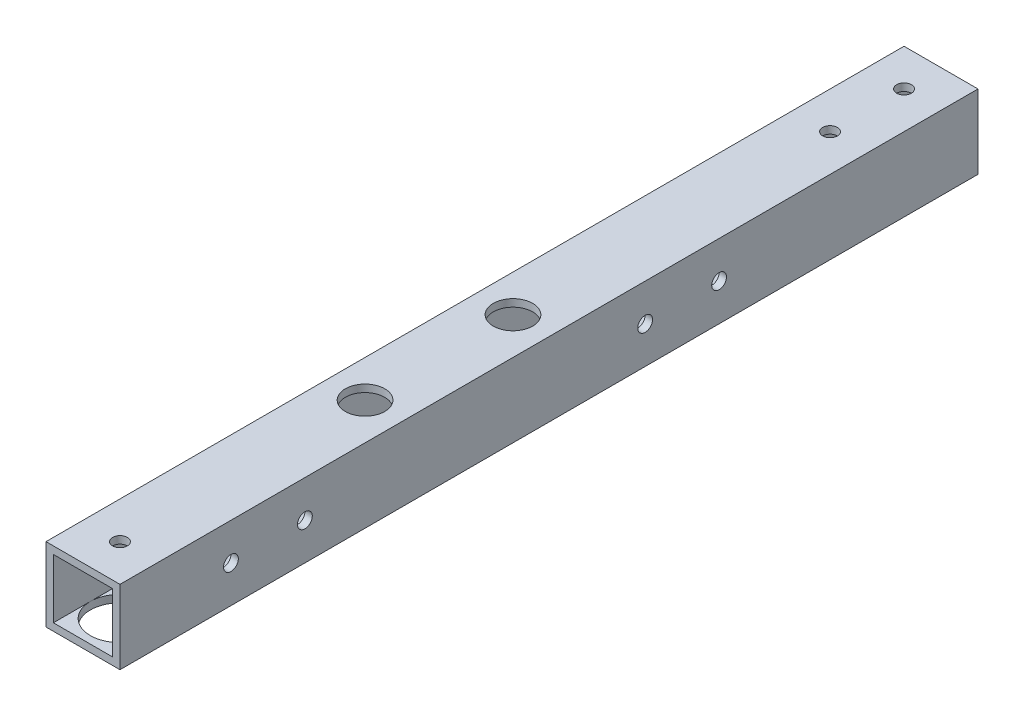
SolidWorks part; units mm, degrees
material "1060 合金"
ref_plane "正面" through (0, 0, 0) normal (0, 0, 1) x (1, 0, 0)
ref_plane "平面" through (0, 0, 0) normal (0, 1, 0) x (1, 0, 0)
ref_plane "右側面" through (0, 0, 0) normal (1, 0, 0) x (0, 0, -1)
sketch "ｽｹｯﾁ1" plane through (0, 0, 0) normal (0, 0, 1) x (1, 0, 0)
  line L1 (-7.0101, 7.7326) -> (7.9899, 7.7326)
  line L2 (-7.0101, 7.7326) -> (-7.0101, -7.2674)
  line L3 (-7.0101, -7.2674) -> (7.9899, -7.2674)
  line L4 (7.9899, 7.7326) -> (7.9899, -7.2674)
  line L9 (-5.5101, 6.2326) -> (6.4899, 6.2326)
  line L10 (-5.5101, 6.2326) -> (-5.5101, -5.7674)
  line L11 (-5.5101, -5.7674) -> (6.4899, -5.7674)
  line L12 (6.4899, 6.2326) -> (6.4899, -5.7674)
  dimension "D1" = 15
  dimension "D2" = 15
  dimension "D3" = 1.5
  dimension "D4" = 1.5
  dimension "D5" = 12
  dimension "D6" = 12
extrude "ﾎﾞｽ - 押し出し2" add sketch "ｽｹｯﾁ1" along normal blind 174
sketch "ｽｹｯﾁ3" plane through (7.9899, 0, 0) normal (1, 0, 0) x (0, 0, -1)
  line L0 (0, 0.2326) -> (-52.5, 0.2326)
  line L1 (0, -7.2674) -> (0, 7.7326) construction
  circle A0 centre (-52.5, 0.2326) radius 1.5
  dimension "D2" = 3
  dimension "D1" = 52.5
extrude "ｶｯﾄ - 押し出し2" cut sketch "ｽｹｯﾁ3" against normal blind 10
sketch "ｽｹｯﾁ6" plane through (-7.0101, 0, 0) normal (-1, 0, 0) x (0, 0, 1)
  line L0 (0, 0.2326) -> (52.5, 0.2326)
  line L1 (0, 7.7326) -> (0, -7.2674) construction
  circle A0 centre (52.5, 0.2326) radius 4
  dimension "D1" = 52.5
extrude "ｶｯﾄ - 押し出し4" cut sketch "ｽｹｯﾁ6" against normal blind 10
sketch "ｽｹｯﾁ7" plane through (7.9899, 0, 0) normal (1, 0, 0) x (0, 0, -1)
  line L0 (-174, 0.2326) -> (-151.5, 0.2326)
  line L1 (-174, -7.2674) -> (-174, 7.7326) construction
  circle A0 centre (-151.5, 0.2326) radius 1.5
  dimension "D1" = 22.5
extrude "ｶｯﾄ - 押し出し5" cut sketch "ｽｹｯﾁ7" against normal blind 10
sketch "ｽｹｯﾁ8" plane through (-7.0101, 0, 0) normal (-1, 0, 0) x (0, 0, 1)
  line L0 (174, 0.2326) -> (151.5, 0.2326)
  line L1 (174, 7.7326) -> (174, -7.2674) construction
  circle A0 centre (151.5, 0.2326) radius 4
  dimension "D1" = 22.5
extrude "ｶｯﾄ - 押し出し6" cut sketch "ｽｹｯﾁ8" against normal blind 10
sketch "ｽｹｯﾁ10" plane through (-7.0101, 0, 0) normal (-1, 0, 0) x (0, 0, 1)
  line L0 (0, 0.2326) -> (86.8, 0.2326)
  line L1 (0, 7.7326) -> (0, -7.2674) construction
  circle A0 centre (86.8, 0.2326) radius 1.5
  dimension "D2" = 3
  dimension "D1" = 86.8
extrude "ｶｯﾄ - 押し出し9" cut sketch "ｽｹｯﾁ10" against normal blind 10
sketch "ｽｹｯﾁ13" plane through (-7.0101, 0, 0) normal (-1, 0, 0) x (0, 0, 1)
  line L0 (86.8, 0.2326) -> (116.8, 0.2326)
  circle A0 centre (116.8, 0.2326) radius 1.5
  dimension "D1" = 30
extrude "ｶｯﾄ - 押し出し11" cut sketch "ｽｹｯﾁ13" against normal blind 10
sketch "ｽｹｯﾁ16" plane through (0, 7.7326, 0) normal (0, 1, 0) x (1, 0, 0)
  line L0 (0.4899, 0) -> (0.4899, -22.5)
  line L1 (7.9899, 0) -> (-7.0101, 0) construction
  circle A0 centre (0.4899, -22.5) radius 1.5
  dimension "D1" = 22.5
extrude "ｶｯﾄ - 押し出し14" cut sketch "ｽｹｯﾁ16" against normal blind 10
sketch "ｽｹｯﾁ17" plane through (0, -7.2674, 0) normal (0, -1, 0) x (1, 0, 0)
  line L0 (0.4899, 174) -> (0.4899, 166.5)
  line L1 (-7.0101, 174) -> (7.9899, 174) construction
  circle A0 centre (0.4899, 166.5) radius 6
  dimension "D1" = 7.5
extrude "ｶｯﾄ - 押し出し15" cut sketch "ｽｹｯﾁ17" against normal blind 10 contours A0
sketch "ｽｹｯﾁ18" plane through (0, 7.7326, 0) normal (0, 1, 0) x (1, 0, 0)
  line L0 (0.4899, -174) -> (0.4899, -166.5)
  line L1 (7.9899, -174) -> (-7.0101, -174) construction
  circle A0 centre (0.4899, -166.5) radius 1.5
  dimension "D1" = 7.5
extrude "ｶｯﾄ - 押し出し16" cut sketch "ｽｹｯﾁ18" against normal blind 10
sketch "ｽｹｯﾁ19" plane through (-7.0101, 0, 0) normal (-1, 0, 0) x (0, 0, 1)
  line L0 (174, -7.2674) -> (0, -7.2674) construction
  circle A0 centre (67.5, 0.2326) radius 4
  circle A1 centre (52.5, 0.2326) radius 4 construction
  dimension "D3" = 8
  dimension "D1" = 7.5
  dimension "D2" = 15
extrude "ｶｯﾄ - 押し出し17" cut sketch "ｽｹｯﾁ19" against normal blind 10
sketch "ｽｹｯﾁ20" plane through (7.9899, 0, 0) normal (1, 0, 0) x (0, 0, -1)
  line L0 (-174, 7.7326) -> (0, 7.7326) construction
  circle A0 centre (-67.5, 0.2326) radius 1.5
  circle A1 centre (-52.5, 0.2326) radius 1.5 construction
  dimension "D1" = 15
  dimension "D2" = 7.5
extrude "ｶｯﾄ - 押し出し18" cut sketch "ｽｹｯﾁ20" against normal blind 10
sketch "ｽｹｯﾁ21" plane through (7.9899, 0, 0) normal (1, 0, 0) x (0, 0, -1)
  circle A0 centre (-136.5, 0.2326) radius 1.5
  circle A1 centre (-151.5, 0.2326) radius 1.5 construction
  dimension "D1" = 15
extrude "ｶｯﾄ - 押し出し19" cut sketch "ｽｹｯﾁ21" against normal blind 10
sketch "ｽｹｯﾁ22" plane through (-7.0101, 0, 0) normal (-1, 0, 0) x (0, 0, 1)
  line L0 (174, -7.2674) -> (0, -7.2674) construction
  circle A0 centre (136.5, 0.2326) radius 4
  circle A1 centre (151.5, 0.2326) radius 4 construction
  dimension "D1" = 15
  dimension "D2" = 7.5
extrude "ｶｯﾄ - 押し出し20" cut sketch "ｽｹｯﾁ22" against normal blind 10
sketch "ｽｹｯﾁ23" plane through (0, 7.7326, 0) normal (0, 1, 0) x (1, 0, 0)
  line L0 (7.9899, 0) -> (-7.0101, 0) construction
  line L1 (-7.0101, -174) -> (-7.0101, 0) construction
  circle A0 centre (0.4899, -7.5) radius 1.5
  dimension "D1" = 7.5
  dimension "D2" = 7.5
extrude "ｶｯﾄ - 押し出し21" cut sketch "ｽｹｯﾁ23" against normal blind 10
sketch "ｽｹｯﾁ24" plane through (0, 7.7326, 0) normal (0, 1, 0) x (1, 0, 0)
  line L0 (7.9899, 0) -> (-7.0101, 0) construction
  line L1 (-7.0101, -174) -> (-7.0101, 0) construction
  circle A0 centre (0.4899, -86.8) radius 4
  dimension "D1" = 86.8
  dimension "D2" = 8
  dimension "D3" = 7.5
extrude "ｶｯﾄ - 押し出し22" cut sketch "ｽｹｯﾁ24" against normal blind 10
sketch "ｽｹｯﾁ25" plane through (0, 7.7326, 0) normal (0, 1, 0) x (1, 0, 0)
  line L0 (-7.0101, -174) -> (-7.0101, 0) construction
  circle A0 centre (0.4899, -116.8) radius 4
  circle A1 centre (0.4899, -86.8) radius 4 construction
  dimension "D1" = 7.5
  dimension "D2" = 30
extrude "ｶｯﾄ - 押し出し23" cut sketch "ｽｹｯﾁ25" against normal blind 10
sketch "ｽｹｯﾁ26" plane through (0, -7.2674, 0) normal (0, -1, 0) x (1, 0, 0)
  line L0 (-7.0101, 0) -> (7.9899, 0) construction
  line L1 (7.9899, 174) -> (7.9899, 0) construction
  circle A0 centre (0.4899, 22.5) radius 6
  point P4 (0.4899, 0)
  dimension "D1" = 22.5
  dimension "D2" = 7.5
extrude "ｶｯﾄ - 押し出し24" cut sketch "ｽｹｯﾁ26" against normal blind 10
